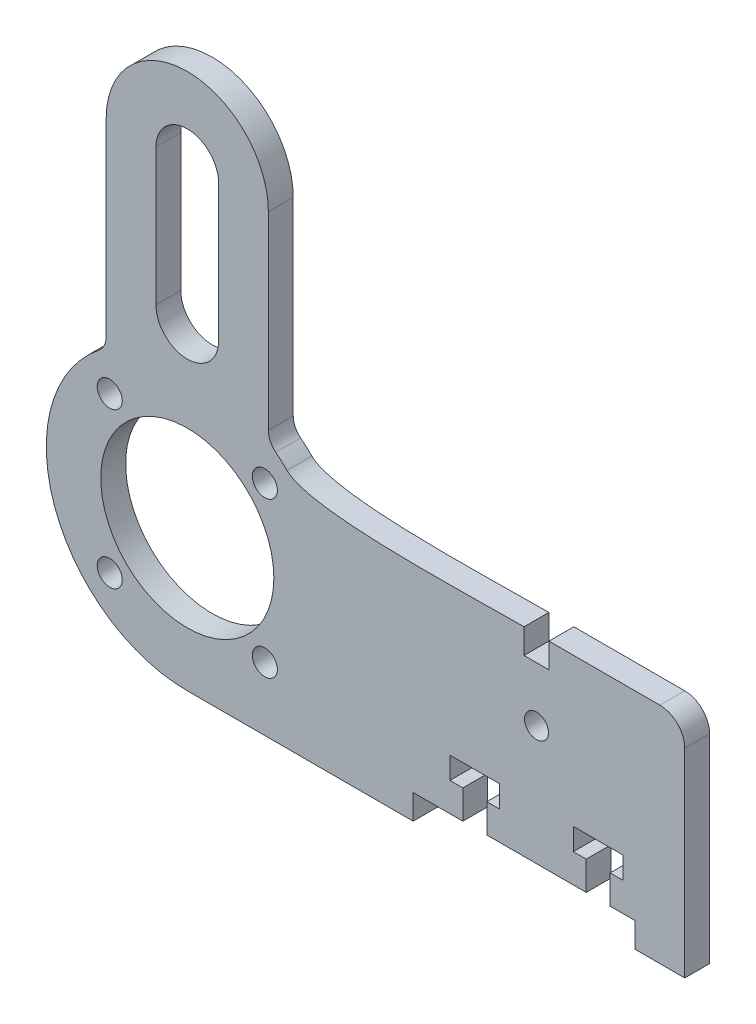
SolidWorks part; units mm, degrees
ref_plane "Front Plane" through (0, 0, 0) normal (0, 0, 1) x (1, 0, 0)
ref_plane "Top Plane" through (0, 0, 0) normal (0, 1, 0) x (1, 0, 0)
ref_plane "Right Plane" through (0, 0, 0) normal (1, 0, 0) x (0, 0, -1)
sketch "Sketch1" plane through (0, 0, 0) normal (0, 0, 1) x (1, 0, 0)
  line L0 (0, 0) -> (12.7277, 12.7277) construction
  line L1 (57.15, -17.9997) -> (63.5, -17.9997)
  line L2 (63.5, -17.9997) -> (63.5, 7.4003)
  line L4 (28.829, -17.9997) -> (28.829, -14.8247)
  line L5 (28.829, -14.8247) -> (35.179, -14.8247)
  line L6 (35.179, -14.8247) -> (35.179, -11.1417)
  line L7 (35.179, -11.1417) -> (33.528, -11.1417)
  line L8 (33.528, -11.1417) -> (33.528, -8.3477)
  line L9 (33.528, -8.3477) -> (39.878, -8.3477)
  line L10 (39.878, -8.3477) -> (39.878, -11.1417)
  line L11 (39.878, -11.1417) -> (38.227, -11.1417)
  line L12 (38.227, -11.1417) -> (38.227, -14.8247)
  line L13 (38.227, -14.8247) -> (50.927, -14.8247)
  line L14 (50.927, -14.8247) -> (50.927, -11.1417)
  line L15 (50.927, -11.1417) -> (49.276, -11.1417)
  line L16 (49.276, -11.1417) -> (49.276, -8.3477)
  line L17 (49.276, -8.3477) -> (55.626, -8.3477)
  line L18 (55.626, -8.3477) -> (55.626, -11.1417)
  line L19 (55.626, -11.1417) -> (53.975, -11.1417)
  line L20 (53.975, -11.1417) -> (53.975, -14.8247)
  line L21 (53.975, -14.8247) -> (57.15, -14.8247)
  line L22 (57.15, -14.8247) -> (57.15, -17.9997)
  line L23 (0, -17.9997) -> (28.829, -17.9997)
  line L24 (42.9895, 10.5753) -> (42.9895, 7.4003)
  line L25 (-10.3505, 15.9911) -> (-10.3505, 40.1261)
  line L26 (10.3505, 15.9911) -> (10.3505, 40.1261)
  line L27 (0, 40.1261) -> (0, 22.6647) construction
  line L28 (4.0005, 40.1261) -> (4.0005, 22.6647)
  line L29 (-4.0005, 40.1261) -> (-4.0005, 22.6647)
  line L30 (25.453, 0.0024) -> (-0.7096, 26.165) construction
  line L31 (65.2545, 10.5753) -> (52.5579, 10.5753) construction
  line L32 (42.9895, 7.4003) -> (46.1645, 7.4003)
  line L33 (46.1645, 7.4003) -> (46.1645, 10.5753)
  line L34 (46.1645, 10.5753) -> (60.325, 10.5753)
  circle A0 centre (0, 0) radius 11.049
  arc A1 (12.7277, 12.7277) -> (11.2964, 14.0136) centre (0, 0) ccw
  circle A2 centre (9.8998, 9.8998) radius 1.6
  circle A3 centre (9.8998, -9.8998) radius 1.6
  circle A4 centre (-9.8998, -9.8998) radius 1.6
  circle A5 centre (-9.8998, 9.8998) radius 1.6
  arc A6 (-10.3505, 40.1261) -> (10.3505, 40.1261) centre (0, 40.1261) cw
  arc A7 (-11.2964, 14.0136) -> (0, -17.9997) centre (0, 0) ccw
  arc A8 (10.3505, 15.9911) -> (11.2964, 14.0136) centre (12.8905, 15.9911) ccw
  arc A9 (-10.3505, 15.9911) -> (-11.2964, 14.0136) centre (-12.8905, 15.9911) cw
  arc A10 (4.0005, 40.1261) -> (-4.0005, 40.1261) centre (0, 40.1261) ccw
  arc A11 (-4.0005, 22.6647) -> (4.0005, 22.6647) centre (0, 22.6647) ccw
  circle A12 centre (44.577, 0.4153) radius 1.524
  arc A13 (60.325, 10.5753) -> (63.5, 7.4003) centre (60.325, 7.4003) cw
  spline S0 degree 3 poles (12.7277, 12.7277) (15.7346, 9.7208) (35.0542, 10.5753) (42.9895, 10.5753) knots 0 0 0 0 1 1 1 1
  point P16 (44.577, 7.4003)
  point P46 (10.3505, 14.7261)
  point P49 (-10.3505, 14.7261)
  point P52 (0, 31.3954)
  point P61 (44.577, -14.8247)
  point P67 (63.5, 10.5753)
  dimension "D1" = 22.098
  dimension "D2" = 35.9994
  dimension "D4" = 3.2
  dimension "D6" = 63.5
  dimension "D7" = 2.794
  dimension "D18" = 2.54
  dimension "D19" = 4.0005
  dimension "D21" = 6.985
  dimension "D23" = 3.048
  dimension "D25" = 3.175
  dimension "D3" = 14.0005
  dimension "D8" = 6.35
  dimension "D9" = 3.048
  dimension "D10" = 12.7
  dimension "D11" = 3.175
  dimension "D12" = 6.477
  dimension "D13" = 6.35
  dimension "D14" = 3.175
  dimension "D15" = 6.35
  dimension "D16" = 20.701
  dimension "D17" = 25.4
  dimension "D20" = 28.575
  dimension "D22" = 3.175
  dimension "D24" = 3.175
  dimension "D5" = 4
extrude "Boss-Extrude1" add sketch "Sketch1" along normal blind 3.175
